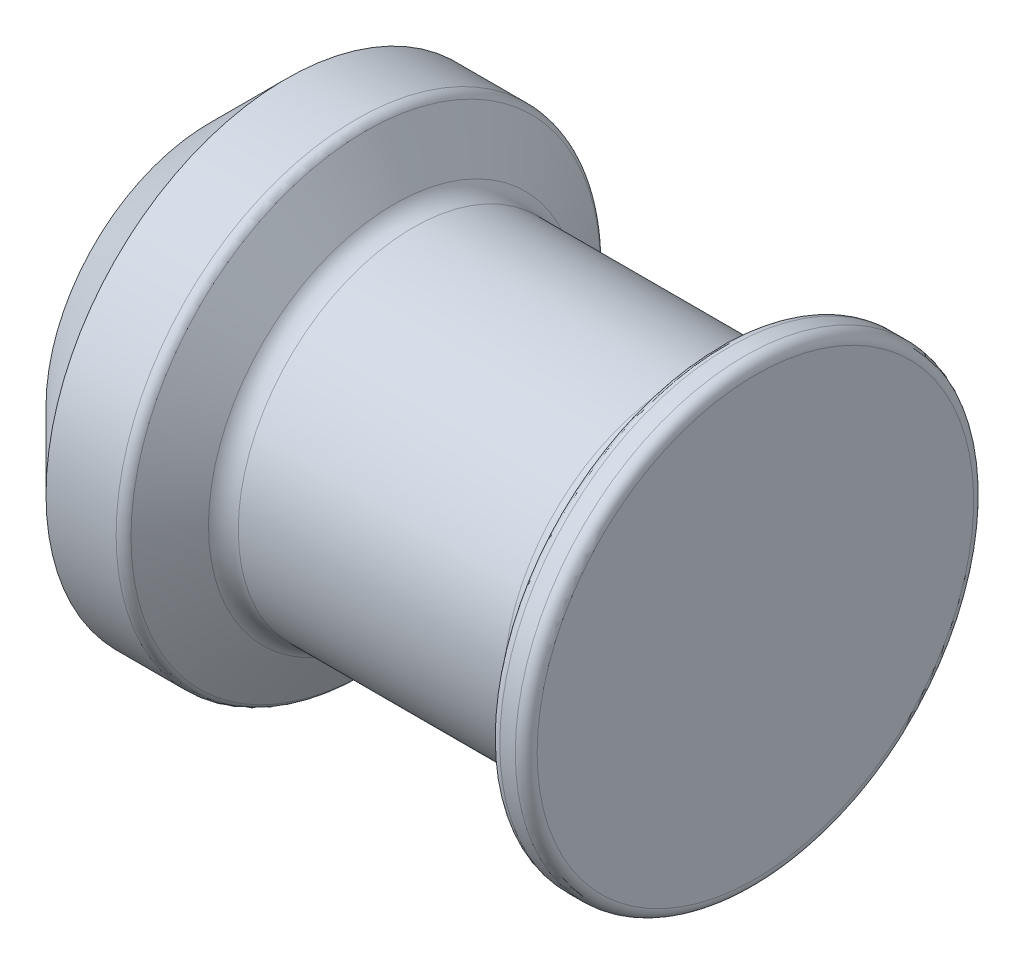
SolidWorks part; units mm, degrees
ref_plane "Plane1" through (0, 0, 0) normal (0, 0, 1) x (1, 0, 0)
ref_plane "Plane2" through (0, 0, 0) normal (0, 1, 0) x (1, 0, 0)
ref_plane "Plane3" through (0, 0, 0) normal (1, 0, 0) x (0, 0, -1)
sketch "Sketch1" plane through (0, 0, 0) normal (0, 0, 1) x (1, 0, 0)
  line L0 (0, 0) -> (50, 0) construction
  line L1 (50, 0) -> (50, 20)
  line L2 (49, 21) -> (47.5774, 21)
  line L3 (46.7113, 20.5) -> (44.6906, 17)
  line L4 (42.9585, 16) -> (18.6188, 16)
  line L5 (16.8868, 17) -> (14.2887, 21.5)
  line L6 (13.4226, 22) -> (7, 22)
  line L7 (7, 22) -> (0, 15)
  line L8 (0, 15) -> (0, 0)
  line L9 (0, 0) -> (50, 0)
  arc A0 (50, 20) -> (49, 21) centre (49, 20) ccw
  arc A1 (47.5774, 21) -> (46.7113, 20.5) centre (47.5774, 20) ccw
  arc A2 (14.2887, 21.5) -> (13.4226, 22) centre (13.4226, 21) ccw
  arc A3 (18.6188, 16) -> (16.8868, 17) centre (18.6188, 18) cw
  arc A4 (44.6906, 17) -> (42.9585, 16) centre (42.9585, 18) cw
  point P14 (47, 21)
  point P17 (14, 22)
  point P20 (17.4641, 16)
  point P23 (44.1132, 16)
  dimension "D12" = 1
  dimension "D13" = 2
  dimension "D1" = 45
  dimension "D2" = 60
  dimension "D3" = 60
  dimension "D4" = 32
  dimension "D5" = 44
  dimension "D6" = 7
  dimension "D7" = 14
  dimension "D8" = 50
  dimension "D9" = 3
  dimension "D10" = 42
  dimension "D11" = 26.6491
revolve "Revolve1" add sketch "Sketch1" angle 360 about L0
